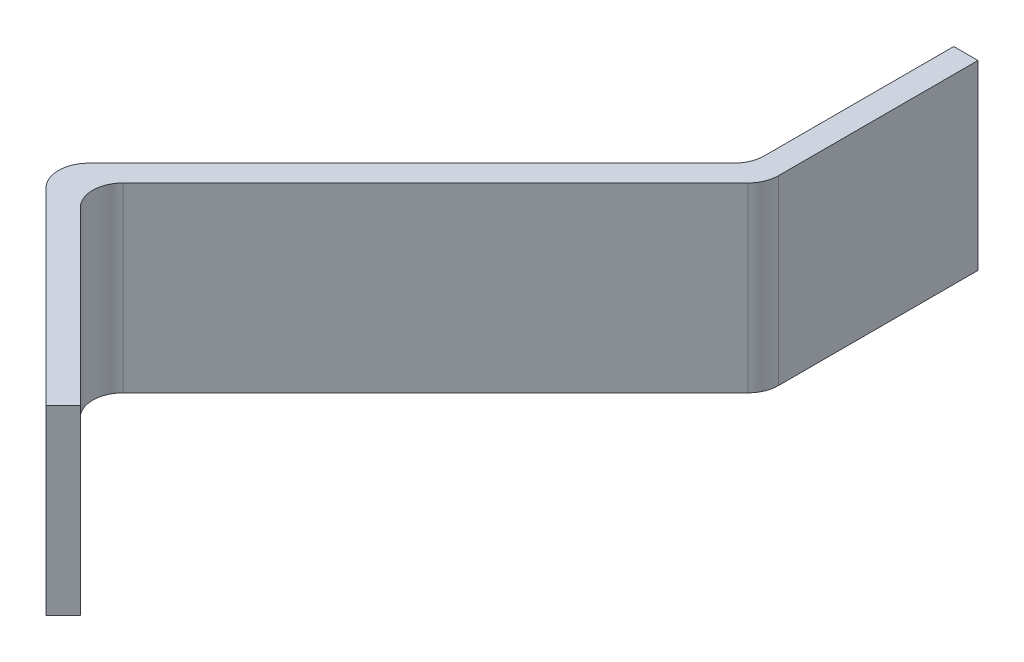
SolidWorks part; units mm, degrees
ref_plane "Front Plane" through (0, 0, 0) normal (0, 0, 1) x (1, 0, 0)
ref_plane "Top Plane" through (0, 0, 0) normal (0, 1, 0) x (1, 0, 0)
ref_plane "Right Plane" through (0, 0, 0) normal (1, 0, 0) x (0, 0, -1)
ref_plane "Plane1" through (0, 7.5, 0) normal (0, 1, 0) x (1, 0, 0)
sketch "Sketch1" plane through (0, 7.5, 0) normal (0, 1, 0) x (1, 0, 0)
  line B0 (-248.7921, -1.7609) -> (-217.6794, -32.8736)
  line B1 (-217.6794, -32.8736) -> (-214.851, -30.0452)
  line B2 (-214.851, -30.0452) -> (-243.1353, -1.7609)
  line B3 (-243.1353, 5.3101) -> (-191.5667, 56.8787)
  line B4 (-190.1023, 60.4142) -> (-190.1023, 93.3431)
  line B5 (-190.1023, 93.3431) -> (-194.1023, 93.3431)
  line B6 (-194.1023, 93.3431) -> (-194.1023, 62.0711)
  line B7 (-195.5667, 58.5355) -> (-248.7921, 5.3101)
  arc B8 (-248.7921, 5.3101) -> (-248.7921, -1.7609) centre (-245.2566, 1.7746) ccw
  arc B9 (-243.1353, 5.3101) -> (-243.1353, -1.7609) centre (-239.5997, 1.7746) ccw
  arc B10 (-191.5667, 56.8787) -> (-190.1023, 60.4142) centre (-195.1023, 60.4142) ccw
  arc B11 (-195.5667, 58.5355) -> (-194.1023, 62.0711) centre (-199.1023, 62.0711) ccw
sketch_block_instance "Block1-1"
sketch_block "Block1" parameters "D1"=0
extrude "Boss-Extrude1" add sketch "Sketch1" against normal blind 30
